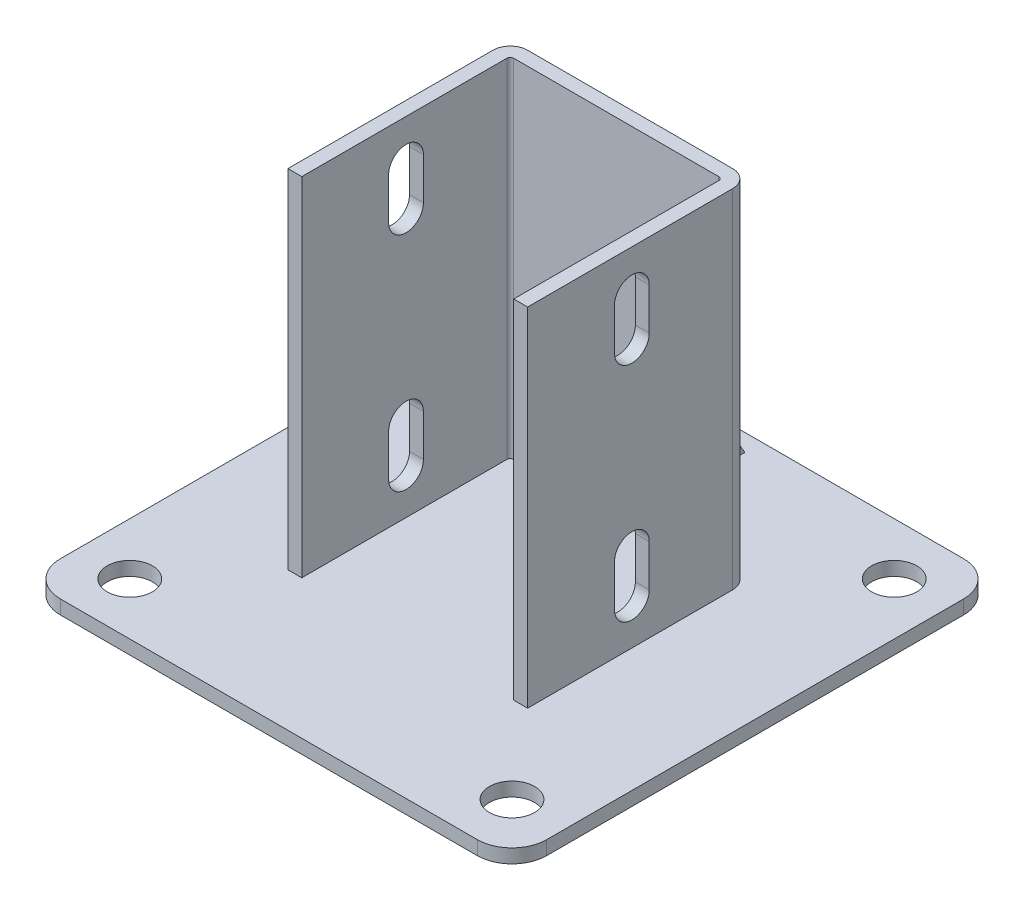
SolidWorks part; units mm, degrees
material "Ст3пс ГОСТ 380-2005"
ref_plane "Спереди" through (0, 0, 0) normal (0, 0, 1) x (1, 0, 0)
ref_plane "Сверху" through (0, 0, 0) normal (0, 1, 0) x (1, 0, 0)
ref_plane "Справа" through (0, 0, 0) normal (1, 0, 0) x (0, 0, -1)
sketch "Эскиз2" plane through (0, 0, 0) normal (0, 1, 0) x (1, 0, 0)
  line L1 (-70, -70) -> (70, -70)
  line L2 (-70, -70) -> (-70, 70)
  line L3 (-70, 70) -> (70, 70)
  line L4 (70, -70) -> (70, 70)
  line L5 (-70, -70) -> (70, 70) construction
  line L6 (-70, 70) -> (70, -70) construction
  point P0 (0, 0)
  dimension "D1" = 140
extrude "Бобышка-Вытянуть1" add sketch "Эскиз2" along normal blind 4
sketch "Эскиз3" plane through (0, 4, 0) normal (0, 1, 0) x (1, 0, 0)
  line L0 (-30.5, -30) -> (-30.5, 30)
  line L1 (-30.5, 30) -> (30.5, 30)
  line L2 (30.5, 30) -> (30.5, -30)
  point P2 (0, 30)
  point P5 (-30.5, 0)
  dimension "D2" = 61
  dimension "D3" = 60
extrude "Вытянуть-Тонкостенный1" add sketch "Эскиз3" along normal offset from surface (100 mm away) 104 thin up to face at (0, 0, 0) thin type one direction reverse wall 4
sketch "Эскиз4" plane through (0, 0, 0) normal (1, 0, 0) x (0, 0, -1)
  line L0 (34, 57.6936) -> (65, 4)
  line L1 (34, 104) -> (34, 4) construction
  line L2 (-70, 4) -> (70, 4) construction
  line L3 (65, 4) -> (34, 4)
  line L4 (34, 4) -> (34, 57.6936)
  line L5 (70, 4) -> (70, 0) construction
  dimension "D1" = 30
  dimension "D2" = 5
extrude "Бобышка-Вытянуть2" add sketch "Эскиз4" along normal mid plane 4
sketch "Эскиз5" plane through (34.5, 0, 0) normal (1, 0, 0) x (0, 0, -1)
  line L0 (0, 92) -> (0, 80) construction
  line L1 (5, 92) -> (5, 80)
  line L2 (-5, 92) -> (-5, 80)
  line L3 (0, 28) -> (0, 16) construction
  line L4 (5, 28) -> (5, 16)
  line L5 (-5, 28) -> (-5, 16)
  line L6 (-30, 104) -> (29, 104) construction
  line L7 (-70, 4) -> (70, 4) construction
  arc A0 (5, 92) -> (-5, 92) centre (0, 92) ccw
  arc A1 (-5, 80) -> (5, 80) centre (0, 80) ccw
  arc A2 (5, 28) -> (-5, 28) centre (0, 28) ccw
  arc A3 (-5, 16) -> (5, 16) centre (0, 16) ccw
  point P3 (0, 86)
  point P8 (0, 22)
  dimension "D2" = 12
  dimension "D4" = 12
  dimension "D1" = 10
  dimension "D3" = 12
extrude "Вырез-Вытянуть1" cut sketch "Эскиз5" against normal through all
sketch "Эскиз6" plane through (0, 4, 0) normal (0, 1, 0) x (1, 0, 0)
  line L0 (-70, 70) -> (-70, -70) construction
  line L1 (55, -55) -> (-55, -55) construction
  line L2 (55, -55) -> (55, 55) construction
  line L3 (55, 55) -> (-55, 55) construction
  line L4 (-55, -55) -> (-55, 55) construction
  line L5 (55, -55) -> (-55, 55) construction
  line L6 (55, 55) -> (-55, -55) construction
  line L7 (70, 70) -> (-70, 70) construction
  circle A0 centre (-55, 55) radius 6.5
  circle A1 centre (-55, -55) radius 6.5
  circle A2 centre (55, 55) radius 6.5
  circle A3 centre (55, -55) radius 6.5
  point P0 (0, 0)
  dimension "D1" = 13
  dimension "D2" = 15
  dimension "D3" = 15
extrude "Вырез-Вытянуть2" cut sketch "Эскиз6" against normal through all
fillet "Скругление1" radius 10 4 edges at (70, 2, 70) (-70, 2, 70) (-70, 2, -70) (70, 2, -70)
